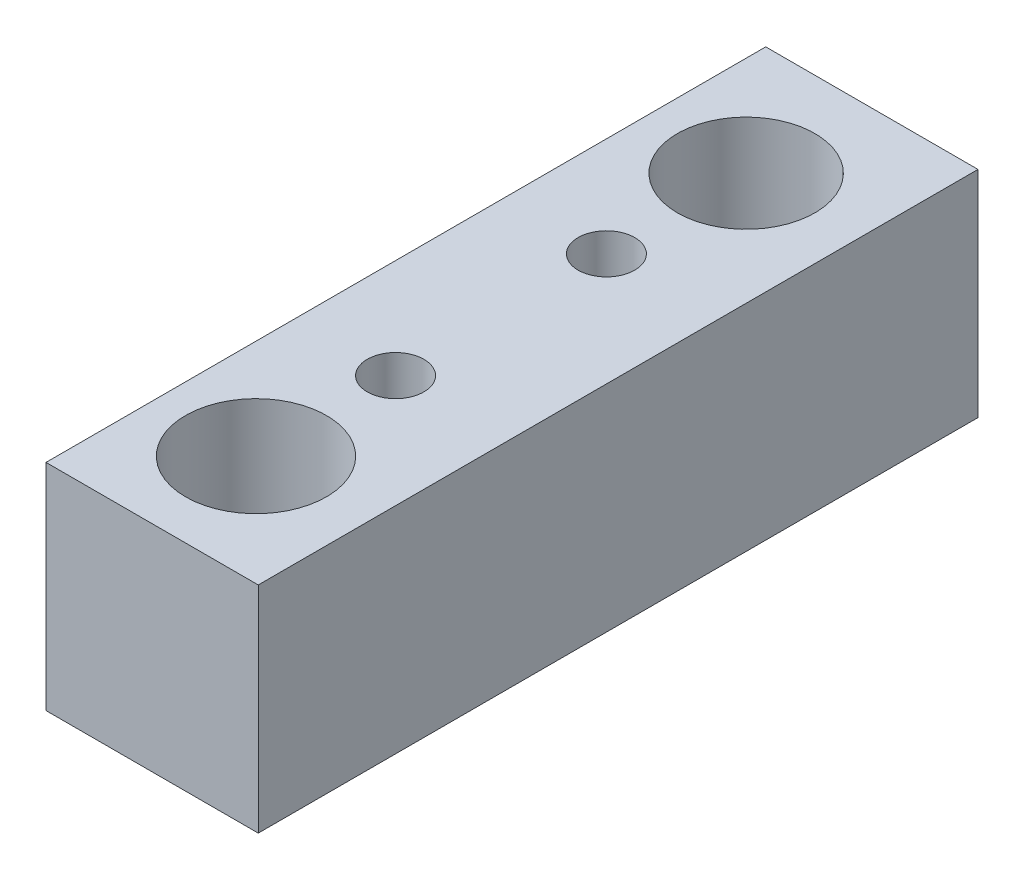
SolidWorks part; units mm, degrees
ref_plane "Front Plane" through (0, 0, 0) normal (0, 0, 1) x (1, 0, 0)
ref_plane "Top Plane" through (0, 0, 0) normal (0, 1, 0) x (1, 0, 0)
ref_plane "Right Plane" through (0, 0, 0) normal (1, 0, 0) x (0, 0, -1)
sketch "Sketch1" plane through (0, 0, 0) normal (1, 0, 0) x (0, 0, -1)
  line L0 (0, 76.6362) -> (0, -98.5883) construction
  line L2 (-181.4966, 0) -> (143.4725, 0) construction
  line L3 (-101.9203, 28.4201) -> (101.5283, 28.4201)
  line L4 (-101.9203, 28.4201) -> (-101.9203, -32.3401)
  line L5 (-101.9203, -32.3401) -> (101.5283, -32.3401)
  line L6 (101.5283, 28.4201) -> (101.5283, -32.3401)
extrude "Boss-Extrude1" add sketch "Sketch1" along normal blind 60
sketch "Sketch2" plane through (0, 28.4201, 0) normal (0, 1, 0) x (-1, 0, 0)
  circle A0 centre (-28.1575, -67.8353) radius 19.4345
  circle A1 centre (-28.1575, 70.7138) radius 19.9238
extrude "Cut-Extrude2" cut sketch "Sketch2" against normal blind 80
sketch "Sketch3" plane through (0, 28.4201, 0) normal (0, 1, 0) x (1, 0, 0)
  circle A0 centre (28.1575, 28.3394) radius 8
  circle A1 centre (28.1575, -31.2661) radius 8
extrude "Cut-Extrude3" cut sketch "Sketch3" against normal blind 45
